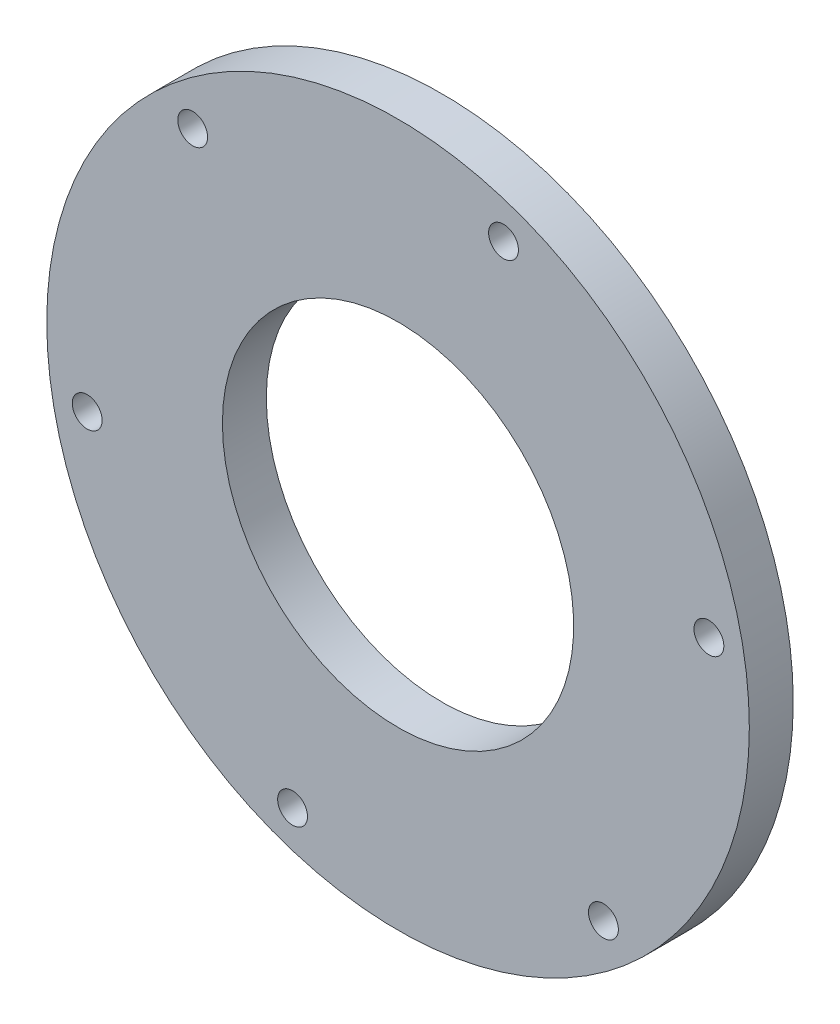
SolidWorks part; units mm, degrees
ref_plane "Front Plane" through (0, 0, 0) normal (0, 0, 1) x (1, 0, 0)
ref_plane "Top Plane" through (0, 0, 0) normal (0, 1, 0) x (1, 0, 0)
ref_plane "Right Plane" through (0, 0, 0) normal (1, 0, 0) x (0, 0, -1)
sketch "Sketch1" plane through (0, 0, 0) normal (0, 0, 1) x (1, 0, 0)
  circle A0 centre (0, 0) radius 40
  dimension "D1" = 80
extrude "Boss-Extrude1" add sketch "Sketch1" along normal blind 5
sketch "Sketch2" plane through (0, 0, 0) normal (0, 0, -1) x (-1, 0, 0)
  circle A0 centre (0, 0) radius 20
  dimension "D1" = 40
extrude "Cut-Extrude1" cut sketch "Sketch2" against normal through all
sketch "Sketch3" plane through (0, 0, 5) normal (0, 0, 1) x (1, 0, 0)
  line L0 (12.0092, 33.9379) -> (13.3436, 37.7087) construction
  circle A0 centre (12.0092, 33.9379) radius 1.7
  circle A1 centre (0, 0) radius 40 construction
  circle A2 centre (35.3957, 6.5687) radius 1.7
  circle A3 centre (23.3864, -27.3692) radius 1.7
  circle A4 centre (-12.0092, -33.9379) radius 1.7
  circle A5 centre (-35.3957, -6.5687) radius 1.7
  circle A6 centre (-23.3864, 27.3692) radius 1.7
  dimension "D1" = 3.4
  dimension "D2" = 4
  dimension "D3" = 6
extrude "Cut-Extrude2" cut sketch "Sketch3" against normal through all
equation "\"mat\"=\"mat@rwv2.assembly\""
equation "\"D1@Boss-Extrude1\"=\"mat\""
